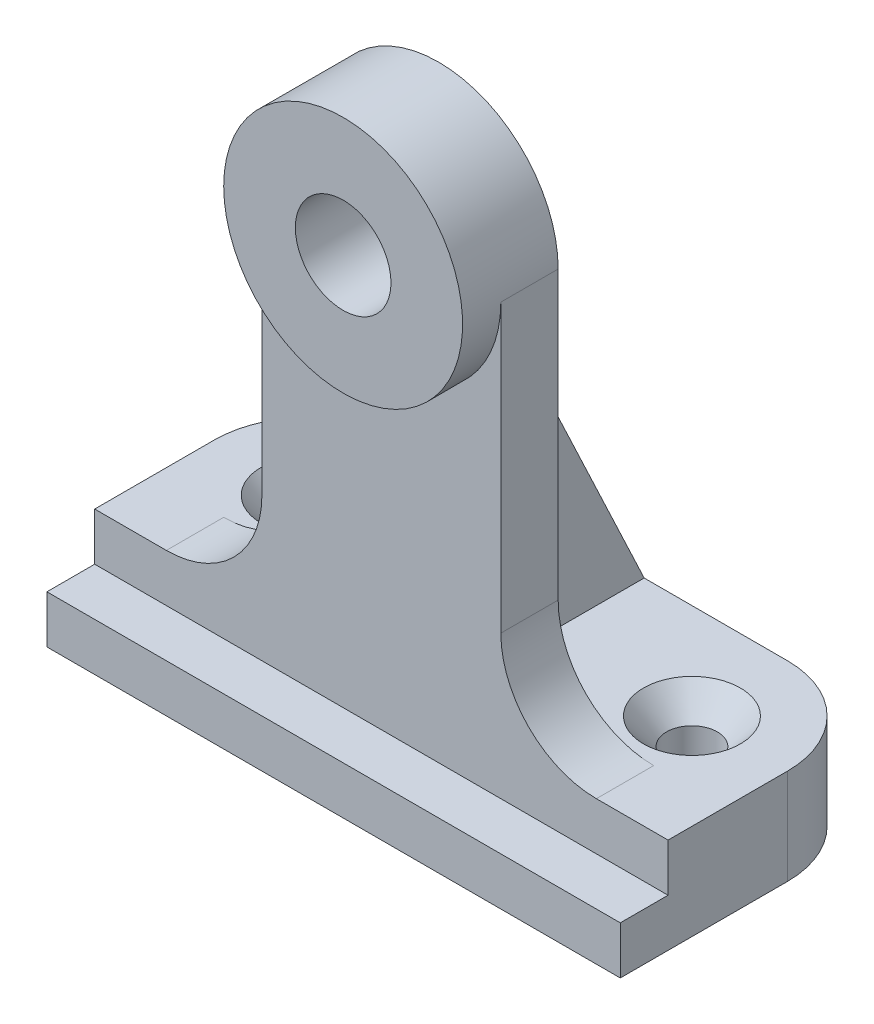
SolidWorks part; units mm, degrees
ref_plane "Front Plane" through (0, 0, 0) normal (0, 0, 1) x (1, 0, 0)
ref_plane "Top Plane" through (0, 0, 0) normal (0, 1, 0) x (1, 0, 0)
ref_plane "Right Plane" through (0, 0, 0) normal (1, 0, 0) x (0, 0, -1)
sketch "Sketch1" plane through (0, 0, 0) normal (0, 1, 0) x (1, 0, 0)
  line L0 (0, 42.3436) -> (0, -11.1125) construction
  line L1 (-25.4, 17.4625) -> (25.4, 17.4625)
  line L2 (-38.1, 4.7625) -> (-38.1, -11.1125)
  line L4 (38.1, 4.7625) -> (38.1, -11.1125)
  line L5 (-80.2591, 0) -> (81.5506, 0) construction
  line L6 (-38.1, -11.1125) -> (38.1, -11.1125)
  arc A0 (25.4, 17.4625) -> (38.1, 4.7625) centre (25.4, 4.7625) cw
  arc A1 (-25.4, 17.4625) -> (-38.1, 4.7625) centre (-25.4, 4.7625) ccw
  point P6 (38.1, 17.4625)
  dimension "D3" = 12.7
  dimension "D1" = 28.575
extrude "Boss-Extrude4" add sketch "Sketch1" along normal blind 12.7
sketch "Sketch10" plane through (0, 0, 0) normal (0, 1, 0) x (1, 0, 0)
  line L1 (-38.1, -11.1125) -> (38.1, -11.1125)
  line L2 (-38.1, -11.1125) -> (-38.1, -17.4625)
  line L3 (-38.1, -17.4625) -> (38.1, -17.4625)
  line L4 (38.1, -11.1125) -> (38.1, -17.4625)
  dimension "D1" = 76.2
  dimension "D2" = 6.35
extrude "Boss-Extrude5" add sketch "Sketch10" along normal blind 6.35
hole_wizard "CSK for 1/4 Flat Head Machine Screw1" positions "Sketch15" profile "Sketch16" countersink size "1/4" standard "ANSI Inch" end condition through all
sketch "Sketch15" plane through (0, 12.7, 0) normal (0, 1, 0) x (1, 0, 0)
  point P0 (-25.4, 4.7625)
  point P3 (25.4, 4.7625)
sketch "Sketch16" plane through (-25.4, 12.7, -4.7625) normal (1, 0, 0) x (0, 0, 1)
  line L0 (0, 0) -> (0, 12.7)
  line L1 (0, 12.7) -> (3.3782, 12.7)
  line L2 (3.3782, 12.7) -> (3.3782, 3.5209)
  line L3 (3.3782, 3.5209) -> (6.4389, 0)
  line L5 (6.4389, 0) -> (0, 0)
  line L6 (-3.3782, 3.5209) -> (-6.4389, 0) construction
  line L11 (0, -6.35) -> (0, 107.95) construction
  dimension "Thru Hole Dia." = 6.7564
  dimension "Thru Hole Depth" = 12.7
  dimension "Near C'Sink Dia." = 12.8778
  dimension "Near C'Sink Angle" = 82
sketch "Sketch19" plane through (0, 0, 11.1125) normal (0, 0, 1) x (1, 0, 0)
  line L0 (0, 0) -> (0, 47.625) construction
  line L1 (-38.1, 12.7) -> (38.1, 12.7) construction
  line L2 (-15.875, 12.7) -> (15.875, 12.7)
  line L3 (-15.875, 12.7) -> (-15.875, 63.5)
  line L5 (15.875, 12.7) -> (15.875, 63.5)
  arc A1 (-15.875, 63.5) -> (15.875, 63.5) centre (0, 63.5) ccw
  dimension "D2" = 31.75
  dimension "D3" = 31.75
extrude "Boss-Extrude6" add sketch "Sketch19" against normal blind 7.62
fillet "Fillet1" radius 12.7 2 edges at (15.875, 12.7, 7.3025) (-15.875, 12.7, 7.3025)
sketch "Sketch20" plane through (0, 0, 3.4925) normal (0, 0, -1) x (-1, 0, 0)
  circle A0 centre (0, 63.5) radius 15.875
  circle A1 centre (0, 63.5) radius 6.35
  dimension "D1" = 31.75
  dimension "D2" = 12.7
extrude "Boss-Extrude7" add sketch "Sketch20" against normal blind 12.7
sketch "Sketch21" plane through (0, 0, 0) normal (1, 0, 0) x (0, 0, -1)
  line L0 (-3.4925, 57.15) -> (17.4625, 12.7)
  line L1 (-3.4925, 25.4) -> (-3.4925, 63.5) construction
  line L2 (17.4625, 12.7) -> (4.7625, 12.7) construction
  line L3 (-3.4925, 57.15) -> (-3.4925, 12.7)
  line L4 (-3.4925, 12.7) -> (17.4625, 12.7)
  dimension "D1" = 20.955
  dimension "D2" = 44.45
extrude "Boss-Extrude8" add sketch "Sketch21" along normal mid plane 12.7
